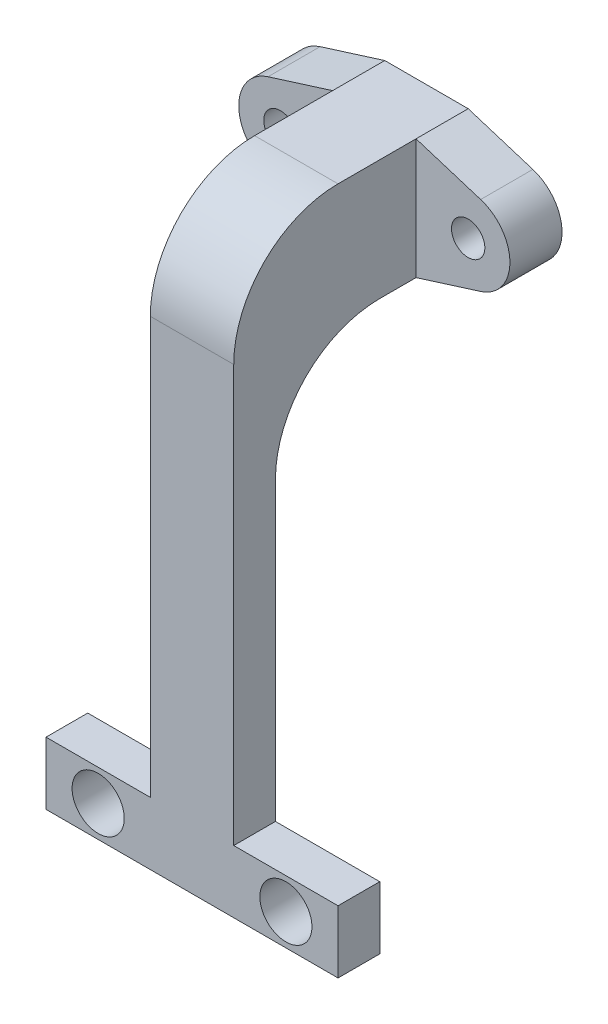
SolidWorks part; units mm, degrees
ref_plane "Front Plane" through (0, 0, 0) normal (0, 0, 1) x (1, 0, 0)
ref_plane "Top Plane" through (0, 0, 0) normal (0, 1, 0) x (1, 0, 0)
ref_plane "Right Plane" through (0, 0, 0) normal (1, 0, 0) x (0, 0, -1)
sketch "Esboço1" plane through (0, 0, 0) normal (0, 0, 1) x (1, 0, 0)
  line L12 (-10.1991, -3.8177) -> (-4, -5.765)
  line L13 (-4, -5.765) -> (4, -5.765)
  line L14 (4, -5.765) -> (10.1978, -3.8173)
  line L15 (10.196, 3.8191) -> (4, 5.763)
  line L16 (4, 5.763) -> (-4, 5.763)
  line L17 (-4, 5.763) -> (-10.1991, 3.8155)
  line L18 (-10.1991, -3.8177) -> (-4, -5.765)
  line L19 (-4, -5.765) -> (4, -5.765)
  line L20 (4, -5.765) -> (10.1978, -3.8173)
  line L21 (10.196, 3.8191) -> (4, 5.763)
  line L22 (4, 5.763) -> (-4, 5.763)
  line L23 (-4, 5.763) -> (-10.1991, 3.8155)
  arc A4 (-10.1991, 3.8155) -> (-10.1991, -3.8177) centre (-9.0001, -0.0011) ccw
  arc A5 (10.1978, -3.8173) -> (10.196, 3.8191) centre (8.998, 0.0006) ccw
  arc A6 (-10.1991, 3.8155) -> (-10.1991, -3.8177) centre (-9.0001, -0.0011) ccw
  arc A7 (10.1978, -3.8173) -> (10.196, 3.8191) centre (8.998, 0.0006) ccw
  circle A8 centre (8.998, 0.0006) radius 1.5982
  circle A9 centre (8.998, 0.0006) radius 1.5982
  circle A11 centre (-9.0001, -0.0011) radius 1.601
  circle A12 centre (-9.0001, -0.0011) radius 1.601
  dimension "D1" = 0
  dimension "D2" = 0
  dimension "D3" = 0
extrude "Ressalto-extrusão1" add sketch "Esboço1" along normal blind 5
sketch "Esboço2" plane through (0, 0, 5) normal (0, 0, 1) x (1, 0, 0)
  line L1 (4, 5.763) -> (-4, 5.763)
  line L2 (4, 5.763) -> (4, -5.765)
  line L3 (4, -5.765) -> (-4, -5.765)
  line L4 (-4, 5.763) -> (-4, -5.765)
extrude "Ressalto-extrusão2" add sketch "Esboço2" along normal up to vertex (17.4804 mm away)
sketch "Esboço3" plane through (0, -5.765, 0) normal (0, -1, 0) x (1, 0, 0)
  line L0 (4, 22.4804) -> (4, 5) construction
  line L1 (-4, 22.4804) -> (4, 22.4804)
  line L2 (-4, 22.4804) -> (-4, 18.4804)
  line L3 (-4, 18.4804) -> (4, 18.4804)
  line L4 (4, 22.4804) -> (4, 18.4804)
  dimension "D1" = 4
extrude "Ressalto-extrusão3" add sketch "Esboço3" along normal up to surface (44.4188 mm away)
sketch "Esboço4" plane through (-4, 0, 0) normal (-1, 0, 0) x (0, 0, 1)
  line L0 (22.4804, 5.763) -> (22.4804, -50.1838) construction
  line L1 (18.4804, -50.1838) -> (22.4804, -50.1838)
  line L2 (18.4804, -50.1838) -> (18.4804, -44.1832)
  line L3 (18.4804, -44.1832) -> (22.4804, -44.1832)
  line L4 (22.4804, -50.1838) -> (22.4804, -44.1832)
extrude "Ressalto-extrusão4" add sketch "Esboço4" along normal blind 10
sketch "Esboço5" plane through (4, 0, 0) normal (1, 0, 0) x (0, 0, -1)
  line L0 (-18.4804, -50.1838) -> (-18.4804, -5.765) construction
  line L1 (-22.4804, -50.1838) -> (-18.4804, -50.1838)
  line L2 (-22.4804, -50.1838) -> (-22.4804, -44.1838)
  line L3 (-22.4804, -44.1838) -> (-18.4804, -44.1838)
  line L4 (-18.4804, -50.1838) -> (-18.4804, -44.1838)
  dimension "D1" = 6
extrude "Ressalto-extrusão5" add sketch "Esboço5" along normal blind 10
fillet "Filete1" radius 10 1 edges at (0, -5.765, 18.4804)
fillet "Filete2" radius 10 1 edges at (0, 5.763, 22.4804)
sketch "Esboço6" plane through (0, 0, 18.4804) normal (0, 0, -1) x (-1, 0, 0)
  line L0 (-14, -47.1838) -> (14, -47.1835) construction
  line L1 (-14, -50.1838) -> (-14, -44.1838) construction
  line L2 (14, -44.1832) -> (14, -50.1838) construction
  circle A0 centre (-9, -47.1838) radius 2.5
  circle A1 centre (9, -47.1836) radius 2.5
  point P10 (0, 0)
  point P11 (0, 0)
  point P12 (0, 0)
  dimension "D1" = 5
  dimension "D2" = 5
  dimension "D3" = 5
  dimension "D4" = 5
extrude "Corte-extrusão1" cut sketch "Esboço6" against normal blind 10
